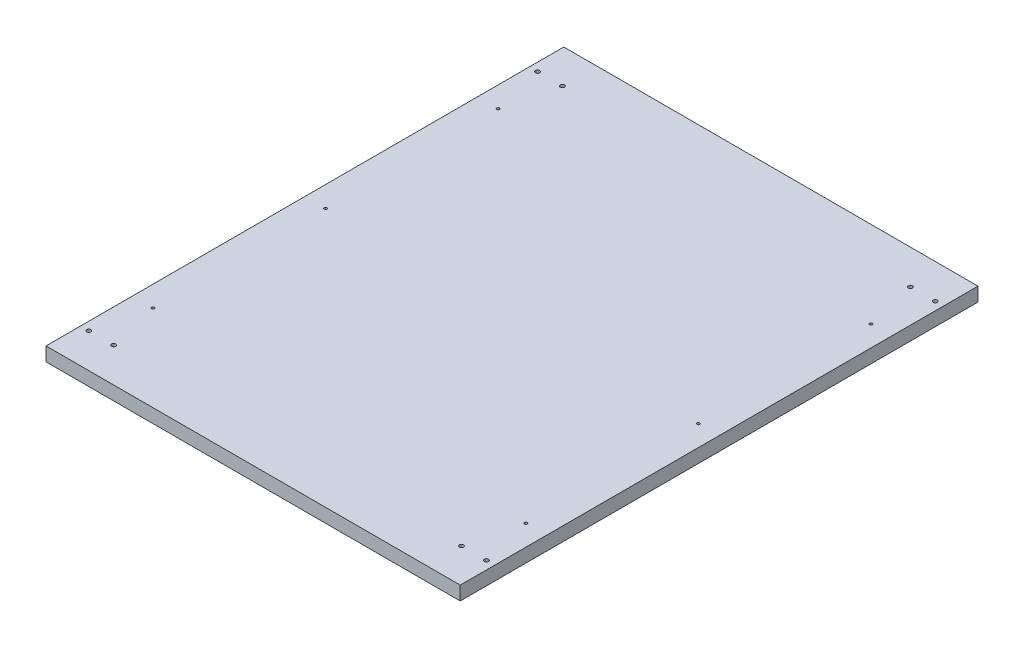
SolidWorks part; units mm, degrees
ref_plane "Front Plane" through (0, 0, 0) normal (0, 0, 1) x (1, 0, 0)
ref_plane "Top Plane" through (0, 0, 0) normal (0, 1, 0) x (1, 0, 0)
ref_plane "Right Plane" through (0, 0, 0) normal (1, 0, 0) x (0, 0, -1)
sketch "Sketch1" plane through (0, 0, 0) normal (0, 1, 0) x (1, 0, 0)
  line L0 (0, 0) -> (600, 0)
  line L1 (600, 0) -> (600, 750)
  line L2 (600, 750) -> (0, 750)
  line L3 (0, 750) -> (0, 0)
  dimension "D1" = 600
  dimension "D2" = 750
extrude "Boss-Extrude1" add sketch "Sketch1" along normal blind 20
sketch "Sketch5" plane through (0, 20, 0) normal (0, 1, 0) x (1, 0, 0)
  circle A0 centre (48, 50) radius 3
  circle A1 centre (12, 50) radius 3
  circle A2 centre (48, 700) radius 3
  circle A3 centre (12, 700) radius 3
  circle A4 centre (552, 50) radius 3
  circle A5 centre (588, 50) radius 3
  circle A6 centre (552, 700) radius 3
  circle A7 centre (588, 700) radius 3
extrude "Cut-Extrude3" cut sketch "Sketch5" against normal through all
sketch "Sketch6" plane through (0, 20, 0) normal (0, 1, 0) x (1, 0, 0)
  circle A0 centre (30, 625) radius 2
  circle A1 centre (570, 625) radius 2
  circle A2 centre (570, 375) radius 2
  circle A3 centre (30, 375) radius 2
  circle A4 centre (30, 125) radius 2
  circle A5 centre (570, 125) radius 2
  dimension "D1" = 4
extrude "Cut-Extrude4" cut sketch "Sketch6" against normal through all
